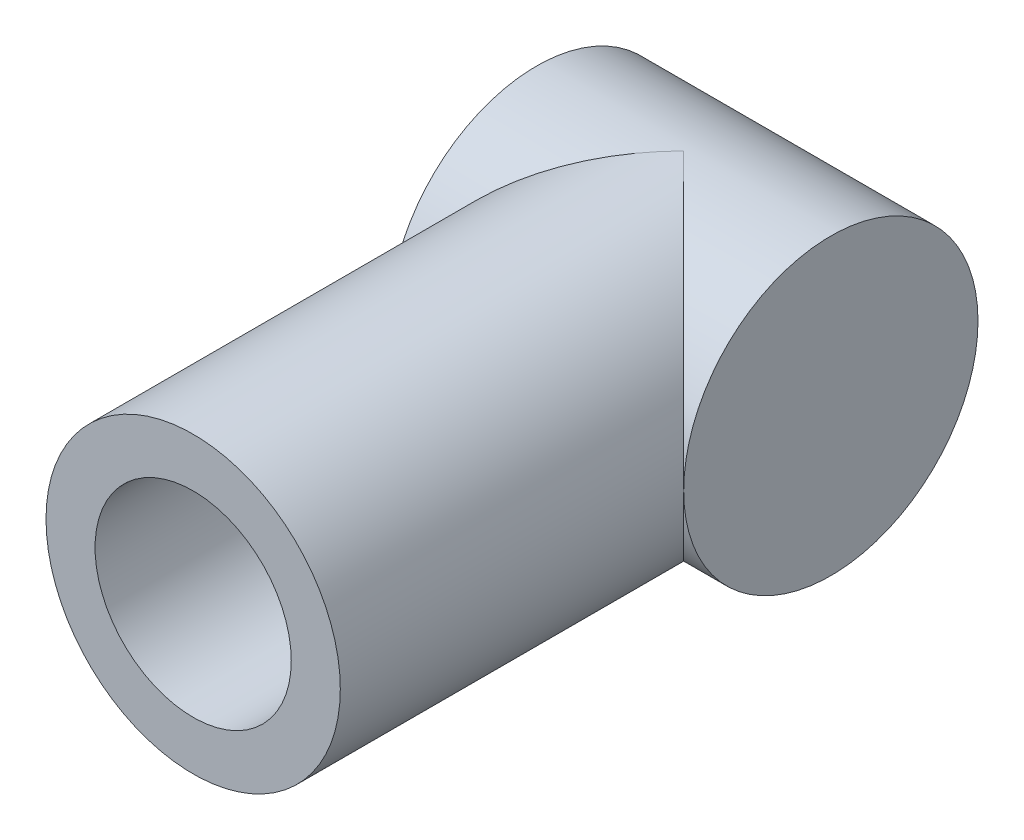
SolidWorks part; units mm, degrees
material "Plain Carbon Steel"
ref_plane "Front Plane" through (0, 0, 0) normal (0, 0, 1) x (1, 0, 0)
ref_plane "Top Plane" through (0, 0, 0) normal (0, 1, 0) x (1, 0, 0)
ref_plane "Right Plane" through (0, 0, 0) normal (1, 0, 0) x (0, 0, -1)
sketch "Sketch1" plane through (0, 0, 0) normal (1, 0, 0) x (0, 0, -1)
  circle A0 centre (0, 0) radius 75
  dimension "D1" = 150
extrude "Boss-Extrude1" add sketch "Sketch1" along normal mid plane 150
sketch "Sketch2" plane through (0, 0, 0) normal (0, 0, 1) x (1, 0, 0)
  circle A0 centre (0, 0) radius 75
  dimension "D1" = 150
extrude "Boss-Extrude2" add sketch "Sketch2" along normal blind 250
sketch "Sketch3" plane through (0, 0, 250) normal (0, 0, 1) x (1, 0, 0)
  circle A0 centre (0, 0) radius 50
  dimension "D1" = 100
extrude "Cut-Extrude1" cut sketch "Sketch3" against normal blind 150
